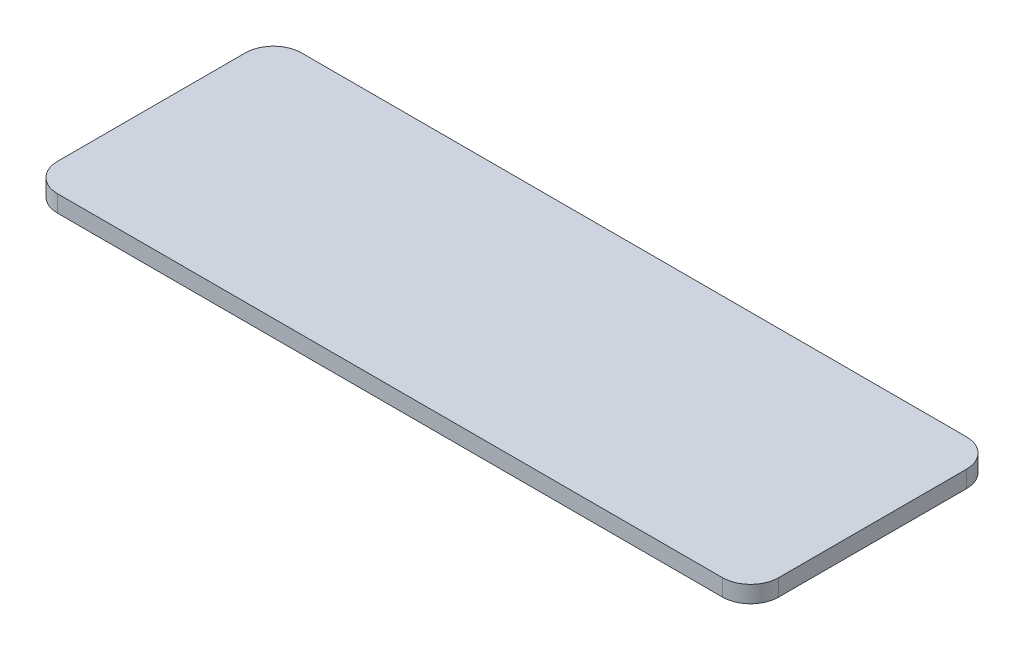
SolidWorks part; units mm, degrees
ref_plane "Front Plane" through (0, 0, 0) normal (0, 0, 1) x (1, 0, 0)
ref_plane "Top Plane" through (0, 0, 0) normal (0, 1, 0) x (1, 0, 0)
ref_plane "Right Plane" through (0, 0, 0) normal (1, 0, 0) x (0, 0, -1)
sketch "Sketch2" plane through (0, 0, 0) normal (0, 1, 0) x (1, 0, 0)
  line L1 (-221.1991, 35.0362) -> (35.2484, 35.0362)
  line L2 (-221.1991, 35.0362) -> (-221.1991, 121.8)
  line L3 (-221.1991, 121.8) -> (35.2484, 121.8)
  line L4 (35.2484, 35.0362) -> (35.2484, 121.8)
  line L5 (-221.1991, 35.0362) -> (35.2484, 121.8) construction
  line L6 (-221.1991, 121.8) -> (35.2484, 35.0362) construction
  point P0 (-92.9754, 78.4181)
extrude "Boss-Extrude2" add sketch "Sketch2" along normal blind 6
fillet "Fillet1" radius 10 4 edges at (-221.1991, 3, -121.8) (35.2484, 3, -121.8) (35.2484, 3, -35.0362) (-221.1991, 3, -35.0362)
